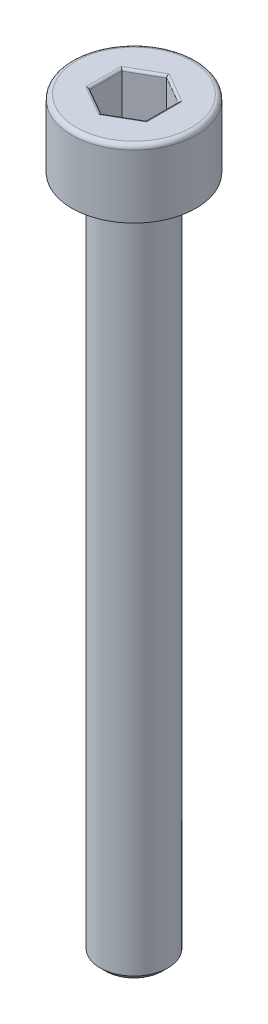
SolidWorks part; units mm, degrees
ref_plane "Front Plane" through (0, 0, 0) normal (0, 0, 1) x (1, 0, 0)
ref_plane "Top Plane" through (0, 0, 0) normal (0, 1, 0) x (1, 0, 0)
ref_plane "Right Plane" through (0, 0, 0) normal (1, 0, 0) x (0, 0, -1)
sketch "Sketch1" plane through (0, 0, 0) normal (0, 0, 1) x (1, 0, 0)
  line L0 (0, 0) -> (0, -47.0967) construction
  line L1 (0, -33) -> (-1.5, -33)
  line L2 (-1.5, -33) -> (-1.5, -3)
  line L3 (-1.5, -3) -> (-2.75, -3)
  line L4 (-2.75, -3) -> (-2.75, 0)
  line L5 (-2.75, 0) -> (0, 0)
  line L6 (0, 0) -> (0, -33)
  dimension "D1" = 30
  dimension "d" = 3
  dimension "k" = 3
  dimension "dk" = 5.5
revolve "Revolve1" add sketch "Sketch1" angle 360 about L0
chamfer "Chamfer1" distance 0.25 angle 45 2 edges at (0, -3, 1.5) (0, -33, 1.5)
fillet "Fillet1" radius 0.2 1 edges at (0, 0, 2.75)
sketch "Sketch2" plane through (0, 0, 0) normal (0, 1, 0) x (1, 0, 0)
  line L1 (0, 1.4434) -> (-1.25, 0.7217)
  line L2 (-1.25, 0.7217) -> (-1.25, -0.7217)
  line L3 (-1.25, -0.7217) -> (0, -1.4434)
  line L4 (0, -1.4434) -> (1.25, -0.7217)
  line L5 (1.25, -0.7217) -> (1.25, 0.7217)
  line L6 (1.25, 0.7217) -> (0, 1.4434)
  circle A0 centre (0, 0) radius 1.25 construction
  dimension "s" = 2.5
extrude "Cut-Extrude1" cut sketch "Sketch2" against normal blind 2
fillet "Fillet2" radius 0.1 12 edges at (-0.625, 0, -1.0825) (-1.25, 0, 0) (-0.625, 0, 1.0825) (0.625, 0, 1.0825) (1.25, 0, 0) (0.625, 0, -1.0825) (1.25, -2, 0) (0.625, -2, 1.0825) (-0.625, -2, 1.0825) (-1.25, -2, 0) (-0.625, -2, -1.0825) (0.625, -2, -1.0825)
